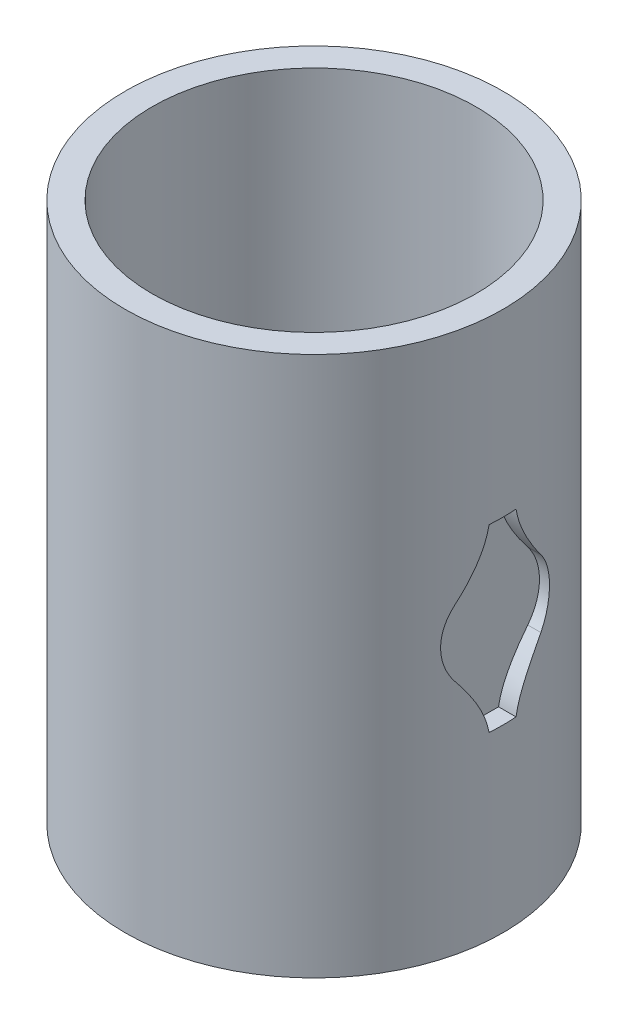
SolidWorks part; units mm, degrees
ref_plane "Front Plane" through (0, 0, 0) normal (0, 0, 1) x (1, 0, 0)
ref_plane "Top Plane" through (0, 0, 0) normal (0, 1, 0) x (1, 0, 0)
ref_plane "Right Plane" through (0, 0, 0) normal (1, 0, 0) x (0, 0, -1)
sketch "Sketch1" plane through (0, 0, 0) normal (0, 1, 0) x (1, 0, 0)
  line L0 (-10.5, 4.9396) -> (-10.5, -4.6359) construction
  line L1 (-14.5, -3) -> (-10.0623, -3)
  line L2 (-14.5, -3) -> (-14.5, 3)
  line L3 (-14.5, 3) -> (-10.0623, 3)
  line L5 (-14.5, 0) -> (0, 0) construction
  line L6 (0, 10.5) -> (0, -10.2883) construction
  line L7 (14.5, -3) -> (10.0623, -3)
  line L8 (14.5, -3) -> (14.5, 3)
  line L9 (14.5, 3) -> (10.0623, 3)
  circle A0 centre (0, 0) radius 9
  circle A1 centre (0, 0) radius 10.5
  dimension "D1" = 18
  dimension "D2" = 1.5
  dimension "D3" = 6
  dimension "D4" = 4
extrude "Boss-Extrude1" add sketch "Sketch1" along normal mid plane 30 contours A1 A0
sketch "Sketch2" plane through (0, 0, 0) normal (1, 0, 0) x (0, 0, -1)
  line L0 (-10.5, 0) -> (10.5, 0) construction
  line L1 (-10.5, 15) -> (-10.5, -15) construction
  line L2 (10.5, -15) -> (10.5, 15) construction
  line L3 (0, 15) -> (0, -15) construction
  line L4 (9, 15) -> (-9, 15) construction
  line L5 (-10.5, -15) -> (10.5, -15) construction
  line L6 (-2.9158, 1.1887) -> (-1.6938, 2.7361) construction
  line L7 (0.75, -5) -> (-0.75, -5)
  line L8 (0.75, -5) -> (0.75, 5)
  line L9 (0.75, 5) -> (-0.75, 5)
  line L10 (-0.75, -5) -> (-0.75, 5)
  line L11 (0.75, -5) -> (-0.75, 5) construction
  line L12 (0.75, 5) -> (-0.75, -5) construction
  circle A0 centre (0, 0) radius 3.025
  spline S0 degree 2 poles (-0.75, 5) (-0.9687, 3.6544) (-2.3741, 1.8747) knots 0 0 0 1 1 1
  spline S1 degree 2 poles (0.75, 5) (0.9687, 3.6544) (2.3741, 1.8747) knots 0 0 0 1 1 1
  spline S2 degree 2 poles (0.75, -5) (0.9687, -3.6544) (2.3741, -1.8747) knots 0 0 0 1 1 1
  spline S3 degree 2 poles (-0.75, -5) (-0.9687, -3.6544) (-2.3741, -1.8747) knots 0 0 0 1 1 1
  dimension "D1" = 6.05
  dimension "D3" = 10
  dimension "D2" = 1.5
extrude "Cut-Extrude1" cut sketch "Sketch2" along normal blind 2 from offset 9.5 contours L10 S0 A0 | L10 A0 | L8 A0 | S1 L8 A0 | L8 S2 A0 | A0 L10 L7 L8 | S3 L10 A0 | A0 L8 L9 L10 | L8 A0 L10
mirror "Mirror1" about plane through (0, 0, 0) normal (1, 0, 0) of "Cut-Extrude1"
